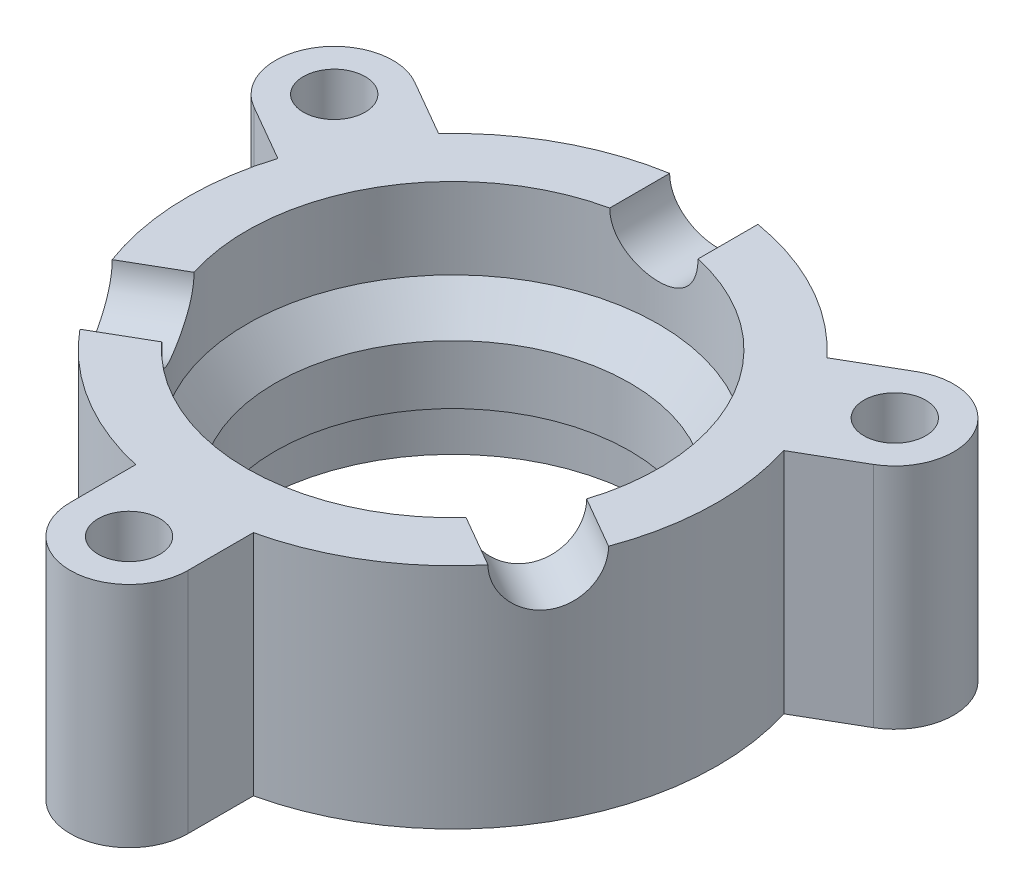
SolidWorks part; units mm, degrees
ref_plane "Front Plane" through (0, 0, 0) normal (0, 0, 1) x (1, 0, 0)
ref_plane "Top Plane" through (0, 0, 0) normal (0, 1, 0) x (1, 0, 0)
ref_plane "Right Plane" through (0, 0, 0) normal (1, 0, 0) x (0, 0, -1)
sketch "Sketch1" plane through (0, 0, 0) normal (0, 1, 0) x (1, 0, 0)
  line L0 (-4, -22) -> (-4, -17.5499)
  line L1 (4, -22) -> (4, -17.5499)
  line L2 (-21.0526, 7.5359) -> (-17.1987, 5.3109)
  line L3 (-17.0526, 14.4641) -> (-13.1987, 12.2391)
  line L4 (17.0526, 14.4641) -> (13.1987, 12.2391)
  line L5 (21.0526, 7.5359) -> (17.1987, 5.3109)
  circle A0 centre (0, 0) radius 18
  circle A1 centre (0, -22) radius 4
  circle A2 centre (0, -22) radius 2.1
  circle A3 centre (-19.0526, 11) radius 4
  circle A4 centre (-19.0526, 11) radius 2.1
  circle A5 centre (19.0526, 11) radius 4
  circle A6 centre (19.0526, 11) radius 2.1
  point P26 (0, 0)
  dimension "D1" = 36
  dimension "D2" = 8
  dimension "D4" = 4.2
  dimension "D3" = 22
  dimension "D5" = 3
extrude "Boss-Extrude1" add sketch "Sketch1" along normal blind 15.5 contours A0 | A1 L1 A0 | A1 A2 | A1 A0 L0 | A3 A0 L3 | A3 L2 A0 | A3 A4 | A5 A6 | A5 A0 L5 | A5 L4 A0
sketch "Sketch2" plane through (0, 15.5, 0) normal (0, 1, 0) x (1, 0, 0)
  circle A0 centre (0, 0) radius 14
  dimension "D1" = 28
extrude "Cut-Extrude1" cut sketch "Sketch2" against normal through all
sketch "Sketch3" plane through (0, 0, 0) normal (0, 0, 1) x (1, 0, 0)
  line L0 (14, 10) -> (12.0587, 7.5)
  line L1 (12.0587, 7.5) -> (12.0587, 3.5)
  line L2 (12.0587, 3.5) -> (13.1987, 3.5)
  line L3 (13.1987, 3.5) -> (13.1987, 0)
  line L4 (13.1987, 0) -> (14, 0)
  line L5 (-14, 0) -> (14, 0) construction
  line L6 (14, 0) -> (14, 10) construction
  line L7 (14, 15.5) -> (-14, 15.5) construction
  line L8 (14, 10) -> (14.4992, 10)
  line L9 (14.4992, 10) -> (14.4992, 0)
  line L10 (14.4992, 0) -> (14, 0)
  dimension "D1" = 5.5
  dimension "D2" = 2.5
  dimension "D3" = 4
  dimension "D4" = 1.14
ref_axis "Axis1" through (0, 0, 0) along (0, 1, 0)
revolve "Revolve1" add sketch "Sketch3" angle 360 about axis through (0, 0, 0) along (0, 1, 0)
sketch "Sketch4" plane through (0, 0, 0) normal (0, 0, 1) x (1, 0, 0)
  line L0 (13.1987, 15.5) -> (-13.1987, 15.5) construction
  circle A0 centre (0, 15.5) radius 3
  dimension "D1" = 6
extrude "Cut-Extrude2" cut sketch "Sketch4" against normal up to surface (17.7482 mm away)
pattern_circular "CirPattern1" count 3 over 360 about axis through (0, 0, 0) along (0, 1, 0) of "Cut-Extrude2"
